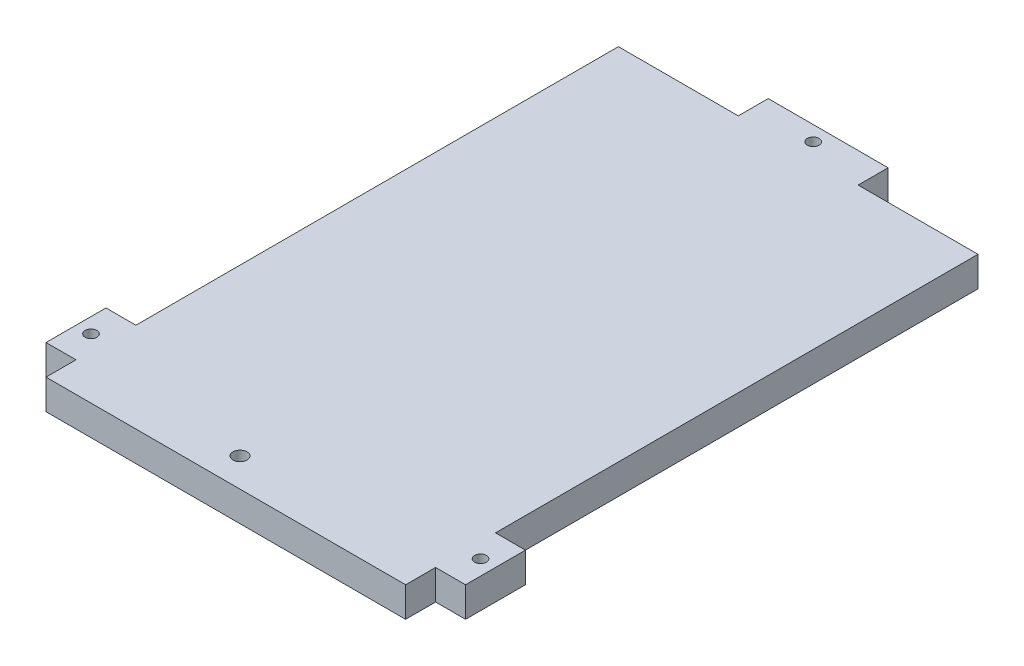
SolidWorks part; units mm, degrees
ref_plane "Front Plane" through (0, 0, 0) normal (0, 0, 1) x (1, 0, 0)
ref_plane "Top Plane" through (0, 0, 0) normal (0, 1, 0) x (1, 0, 0)
ref_plane "Right Plane" through (0, 0, 0) normal (1, 0, 0) x (0, 0, -1)
sketch "Sketch1" plane through (0, 0, 0) normal (0, 1, 0) x (1, 0, 0)
  line L0 (50.8, 121.285) -> (76.2, 121.285)
  line L1 (0, 0) -> (76.2, 0)
  line L2 (0, 0) -> (0, 6.35)
  line L3 (0, 121.285) -> (25.4, 121.285)
  line L4 (76.2, 0) -> (76.2, 6.35)
  line L5 (0, 19.05) -> (0, 121.285)
  line L6 (25.4, 121.285) -> (25.4, 127.635)
  line L7 (25.4, 127.635) -> (50.8, 127.635)
  line L8 (50.8, 121.285) -> (50.8, 127.635)
  line L9 (0, 19.05) -> (-6.35, 19.05)
  line L10 (76.2, 19.05) -> (76.2, 121.285)
  line L11 (0, 6.35) -> (-6.35, 6.35)
  line L12 (-6.35, 19.05) -> (-6.35, 6.35)
  line L13 (76.2, 19.05) -> (82.55, 19.05)
  line L15 (76.2, 6.35) -> (82.55, 6.35)
  line L16 (82.55, 19.05) -> (82.55, 6.35)
  dimension "D1" = 76.2
  dimension "D2" = 6.35
  dimension "D3" = 6.35
  dimension "D4" = 6.35
  dimension "D5" = 6.35
  dimension "D6" = 12.7
  dimension "D7" = 12.7
  dimension "D8" = 121.285
  dimension "D9" = 25.4
  dimension "D10" = 6.35
extrude "Boss-Extrude1" add sketch "Sketch1" along normal blind 6.35
sketch "Sketch2" plane through (0, 6.35, 0) normal (0, 1, 0) x (1, 0, 0)
  line L0 (35.0139, 6.096) -> (35.0139, 0) construction
  line L1 (0, 0) -> (76.2, 0) construction
  line L2 (35.0139, 6.096) -> (0, 6.096) construction
  line L3 (0, 6.35) -> (0, 0) construction
  circle A0 centre (35.0139, 6.096) radius 1.5
  dimension "D1" = 3
  dimension "D2" = 6.096
  dimension "D3" = 35.0139
extrude "Cut-Extrude1" cut sketch "Sketch2" against normal through all
sketch "Sketch3" plane through (0, 6.35, 0) normal (0, 1, 0) x (1, 0, 0)
  line L0 (-3.175, 19.05) -> (-3.175, 12.7) construction
  line L1 (0, 19.05) -> (-6.35, 19.05) construction
  line L2 (79.375, 19.05) -> (79.375, 12.7) construction
  line L3 (82.55, 19.05) -> (76.2, 19.05) construction
  line L4 (79.375, 6.35) -> (79.375, 12.7) construction
  line L5 (76.2, 6.35) -> (82.55, 6.35) construction
  line L6 (25.4, 124.46) -> (38.1, 124.46) construction
  line L7 (-3.175, 6.35) -> (-3.175, 12.7) construction
  line L8 (-6.35, 6.35) -> (0, 6.35) construction
  line L9 (25.4, 127.635) -> (25.4, 121.285) construction
  line L10 (38.1, 124.46) -> (50.8, 124.46) construction
  line L11 (50.8, 121.285) -> (50.8, 127.635) construction
  circle A0 centre (-3.175, 12.7) radius 1.25
  circle A1 centre (79.375, 12.7) radius 1.25
  circle A2 centre (38.1, 124.46) radius 1.25
  dimension "D1" = 2.5
extrude "Cut-Extrude2" cut sketch "Sketch3" against normal through all
